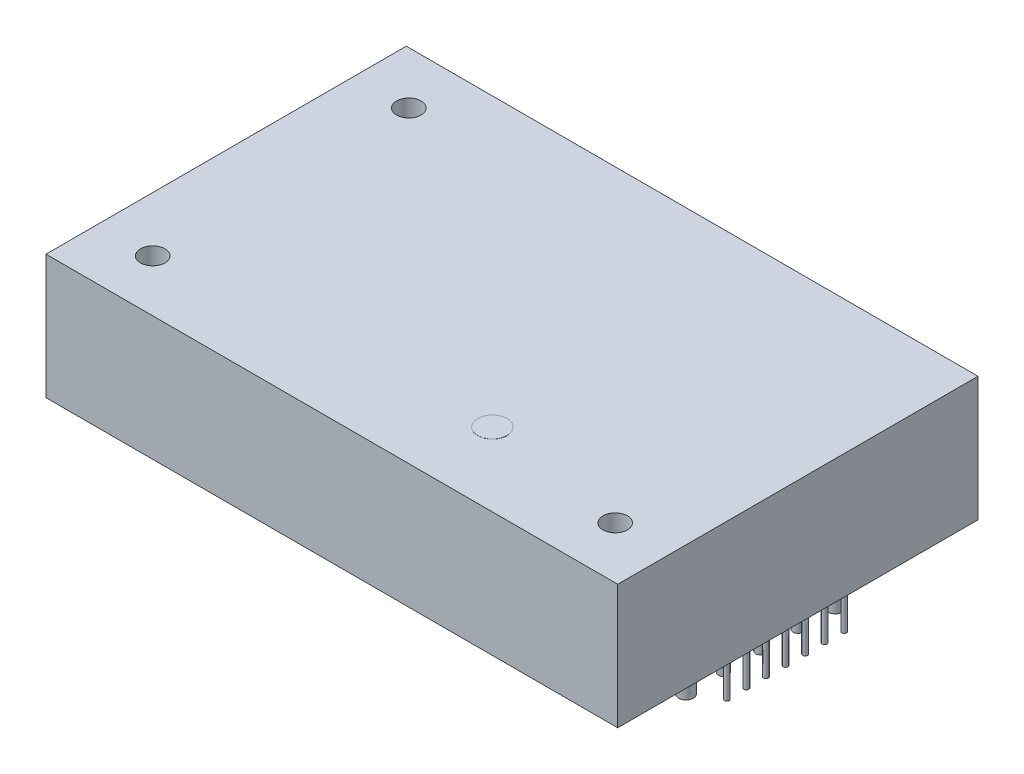
SolidWorks part; units mm, degrees
ref_plane "Front Plane" through (0, 0, 0) normal (0, 0, 1) x (1, 0, 0)
ref_plane "Top Plane" through (0, 0, 0) normal (0, 1, 0) x (1, 0, 0)
ref_plane "Right Plane" through (0, 0, 0) normal (1, 0, 0) x (0, 0, -1)
sketch "Sketch1" plane through (0, 0, 0) normal (0, 1, 0) x (1, 0, 0)
  line L1 (29.2, 18.4) -> (-29.2, 18.4)
  line L2 (29.2, 18.4) -> (29.2, -18.4)
  line L3 (29.2, -18.4) -> (-29.2, -18.4)
  line L4 (-29.2, 18.4) -> (-29.2, -18.4)
  line L5 (29.2, 18.4) -> (-29.2, -18.4) construction
  line L6 (29.2, -18.4) -> (-29.2, 18.4) construction
  point P0 (0, 0)
  dimension "D1" = 36.8
  dimension "D2" = 58.4
extrude "Boss-Extrude1" add sketch "Sketch1" along normal blind 12.7
sketch "Sketch2" plane through (0, 0, 0) normal (0, -1, 0) x (1, 0, 0)
  line L0 (-29.2, -18.4) -> (-29.2, 18.4) construction
  line L1 (27.94, 0) -> (27.94, -2) construction
  circle A0 centre (-25.4, 0) radius 0.5
  circle A1 centre (-25.4, 3.81) radius 0.5
  circle A2 centre (-25.4, 7.62) radius 0.5
  circle A3 centre (-25.4, -7.62) radius 0.5
  circle A4 centre (25.4, 7.62) radius 0.75
  circle A5 centre (25.4, 3.81) radius 0.5
  circle A6 centre (25.4, 0) radius 0.5
  circle A7 centre (25.4, -3.81) radius 0.5
  circle A8 centre (25.4, -7.62) radius 0.75
  circle A9 centre (27.94, 0) radius 0.25
  circle A10 centre (27.94, -2) radius 0.25
  circle A11 centre (27.94, -4) radius 0.25
  circle A12 centre (27.94, -6) radius 0.25
  circle A13 centre (27.94, 0) radius 0.25
  circle A14 centre (27.94, -2) radius 0.25
  circle A15 centre (27.94, -4) radius 0.25
  circle A16 centre (27.94, 2) radius 0.25
  circle A17 centre (27.94, 0) radius 0.25
  circle A18 centre (27.94, -2) radius 0.25
  circle A19 centre (27.94, 4) radius 0.25
  circle A20 centre (27.94, 2) radius 0.25
  circle A21 centre (27.94, 0) radius 0.25
  circle A22 centre (27.94, 2) radius 0.25
  circle A23 centre (27.94, 4) radius 0.25
  circle A24 centre (27.94, 6) radius 0.25
  dimension "D1" = 1
  dimension "D6" = 1.5
  dimension "D7" = 1
  dimension "D10" = 0.5
  dimension "D2" = 3.8
  dimension "D3" = 7.62
  dimension "D4" = 11.43
  dimension "D5" = 15.24
  dimension "D8" = 3.81
  dimension "D9" = 50.8
  dimension "D11" = 2.54
  dimension "D14" = 2
  dimension "D12" = 4
  dimension "D13" = 4
extrude "Boss-Extrude2" add sketch "Sketch2" along normal blind 4.3
sketch "Sketch3" plane through (0, 12.7, 0) normal (0, 1, 0) x (1, 0, 0)
  line L0 (-29.2, 18.4) -> (-29.2, -18.4) construction
  line L2 (-29.2, -18.4) -> (29.2, -18.4) construction
  point P0 (-23.6, 13.06)
  point P1 (-23.6, -13.1)
  point P2 (23.64, -13.1)
  dimension "D1" = 5.6
  dimension "D2" = 5.3
  dimension "D3" = 26.16
  dimension "D4" = 47.24
hole_wizard "M3x0.5 Tapped Hole1" positions "3DSketch1" profile "Sketch5" tap size "M3x0.5" standard "ANSI Metric"
sketch3d "3DSketch1"
  point P0 (-23.6, 12.7, -13.06)
  point P3 (-23.6, 12.7, 13.1)
  point P6 (23.64, 12.7, 13.1)
sketch "Sketch5" plane through (-23.6, 12.7, -13.06) normal (1, 0, 0) x (0, 0, 1)
  line L0 (0, 0) -> (0, 5.2511)
  line L1 (0, 5.2511) -> (1.25, 4.5)
  line L2 (1.25, 4.5) -> (1.25, 0)
  line L5 (1.25, 0) -> (0, 0)
  line L10 (0, 5.2511) -> (-1.25, 4.5) construction
  line L11 (0, -6.35) -> (0, 107.95) construction
  dimension "Tap Drill Dia." = 2.5
  dimension "Tap Drill Depth" = 4.5
  dimension "Drill Angle" = 118
cosmetic thread "Hole Thread1" parameters "D1"=3, "D2"=3
cosmetic thread "Hole Thread2" parameters "D1"=3, "D2"=3
cosmetic thread "Hole Thread3" parameters "D1"=3, "D2"=3
sketch "Sketch6" plane through (0, 12.7, 0) normal (0, 1, 0) x (1, 0, 0)
  line L0 (-29.2, -18.4) -> (29.2, -18.4) construction
  line L1 (-29.2, 18.4) -> (-29.2, -18.4) construction
  circle A0 centre (8.9, -10.9) radius 1.5
  point P0 (8.9, -10.9)
  dimension "D3" = 3
  dimension "D1" = 7.5
  dimension "D2" = 38.1
extrude "Boss-Extrude3" add sketch "Sketch6" along normal blind 0.01 contours A0
